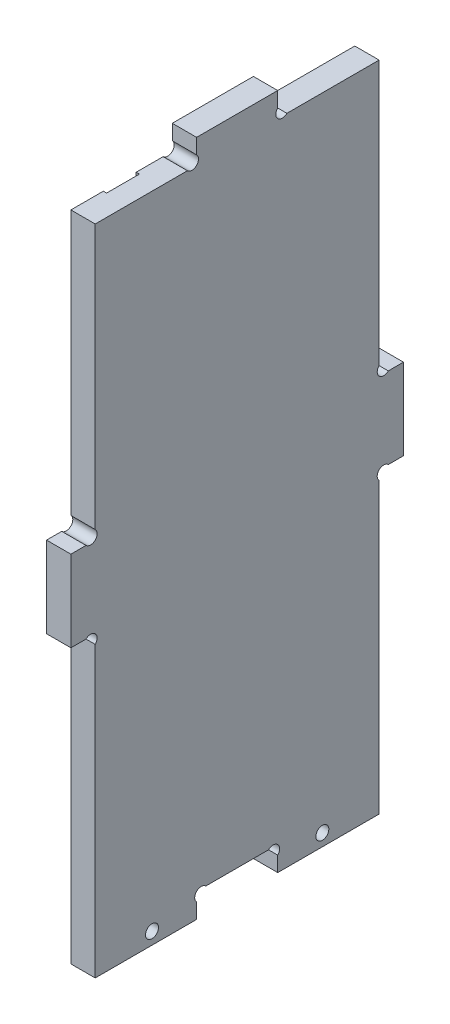
SolidWorks part; units mm, degrees
ref_plane "Plan de face" through (0, 0, 0) normal (0, 0, 1) x (1, 0, 0)
ref_plane "Plan de dessus" through (0, 0, 0) normal (0, 1, 0) x (1, 0, 0)
ref_plane "Plan de droite" through (0, 0, 0) normal (1, 0, 0) x (0, 0, -1)
sketch "Esquisse1" plane through (0, 0, 0) normal (1, 0, 0) x (0, 0, -1)
  line L0 (0, -30.7196) -> (0, 229.7017) construction
  line L1 (-9.0406, 0) -> (101.3462, 0) construction
  line L2 (-35.0297, 167) -> (123.1673, 167) construction
  line L3 (82, -30.7196) -> (82, 229.7017) construction
  line L4 (-35.0297, 6) -> (101.3462, 6) construction
  line L5 (-35.0297, 161) -> (101.3462, 161) construction
  line L6 (41, 198.0917) -> (41, -21.4572) construction
  line L7 (6, 213.5209) -> (6, -30.7196) construction
  line L8 (-35.0297, 83.5) -> (17.0365, 83.5) construction
  line L9 (17.0365, 73.5) -> (-35.0297, 73.5) construction
  line L10 (51, 181.2829) -> (51, 156.4029) construction
  line L11 (6, 73.5) -> (-20.8335, 46.6665) construction
  line L12 (3.7373, 73.5) -> (0, 73.5)
  line L13 (6, 71.2373) -> (6, 0)
  line L15 (3.7373, 93.5) -> (0, 93.5)
  line L16 (0, 93.5) -> (0, 73.5)
  line L17 (82, 93.5) -> (82, 73.5)
  line L18 (78.2627, 93.5) -> (82, 93.5)
  line L19 (78.2627, 73.5) -> (82, 73.5)
  line L20 (76, 189.4071) -> (76, -10.8473) construction
  line L21 (51, 163.2627) -> (51, 167)
  line L22 (51, 167) -> (31, 167)
  line L23 (31, 10.7132) -> (31, -21.4572) construction
  line L24 (31, 6) -> (49.7877, -12.7877) construction
  line L25 (-9.0406, 3) -> (23.2288, 3) construction
  line L26 (51, 161) -> (69.8431, 179.8431) construction
  line L27 (20, -21.4572) -> (20, 10.7132) construction
  line L28 (6, 0) -> (31, 0)
  line L29 (31, 0) -> (31, 3.7373)
  line L30 (33.2627, 6) -> (48.7373, 6)
  line L31 (51, 3.7373) -> (51, 0)
  line L32 (51, 0) -> (76, 0)
  line L33 (31, 167) -> (31, 163.2627)
  line L34 (28.7373, 161) -> (6, 161)
  line L35 (6, 161) -> (6, 95.7627)
  line L37 (53.2627, 161) -> (76, 161)
  line L45 (76, 71.2373) -> (76, 0)
  line L46 (76, 95.7627) -> (76, 161)
  arc A0 (76, 95.7627) -> (78.2627, 93.5) centre (77.1314, 94.6314) ccw
  arc A1 (6, 71.2373) -> (3.7373, 73.5) centre (4.8686, 72.3686) ccw
  arc A2 (6, 95.7627) -> (3.7373, 93.5) centre (4.8686, 94.6314) cw
  arc A3 (76, 71.2373) -> (78.2627, 73.5) centre (77.1314, 72.3686) cw
  arc A4 (51, 163.2627) -> (53.2627, 161) centre (52.1314, 162.1314) ccw
  arc A5 (31, 163.2627) -> (28.7373, 161) centre (29.8686, 162.1314) cw
  circle A6 centre (20, 3) radius 1.6
  arc A7 (33.2627, 6) -> (31, 3.7373) centre (32.1314, 4.8686) ccw
  arc A8 (48.7373, 6) -> (51, 3.7373) centre (49.8686, 4.8686) cw
  circle A9 centre (62, 3) radius 1.6
  dimension "D9" = 10
  dimension "D1" = 82
  dimension "D2" = 155
  dimension "D3" = 41
  dimension "D4" = 6
  dimension "D5" = 6
  dimension "D6" = 6
  dimension "D7" = 77.5
  dimension "D8" = 10
  dimension "D10" = 45
  dimension "D12" = 10
  dimension "D13" = 45
  dimension "D14" = 45
  dimension "D15" = 3
  dimension "D16" = 11
extrude "Boss.-Extru.1" add sketch "Esquisse1" along normal blind 6
sketch "Esquisse2" plane through (0, 0, 0) normal (-1, 0, 0) x (0, 0, 1)
  line L0 (-6, 190.4744) -> (-6, -14.3981) construction
  line L1 (-2.9516, 6) -> (-72.7833, 6) construction
  line L3 (-14, 216.2064) -> (-14, -14.3981) construction
  line L4 (-22.1, 216.2064) -> (-22.1, -14.3981) construction
  line L5 (-18.05, -5.7481) -> (-18.05, 5.2044) construction
  line L6 (-22.1, 165.8611) -> (-14, 165.8611)
  line L7 (-22.1, 165.8611) -> (-22.1, 8.2627)
  line L8 (-19.8373, 6) -> (-16.2627, 6)
  line L9 (-14, 165.8611) -> (-14, 8.2627)
  line L10 (-22.1, 6) -> (-13.9019, 14.1981) construction
  arc A0 (-22.1, 8.2627) -> (-19.8373, 6) centre (-20.9686, 7.1314) ccw
  arc A1 (-14, 8.2627) -> (-16.2627, 6) centre (-15.1314, 7.1314) cw
  dimension "D1" = 8
  dimension "D2" = 8.1
  dimension "D3" = 4.05
  dimension "D4" = 45
extrude "Enlèv. mat.-Extru.1" cut sketch "Esquisse2" against normal blind 0.8
